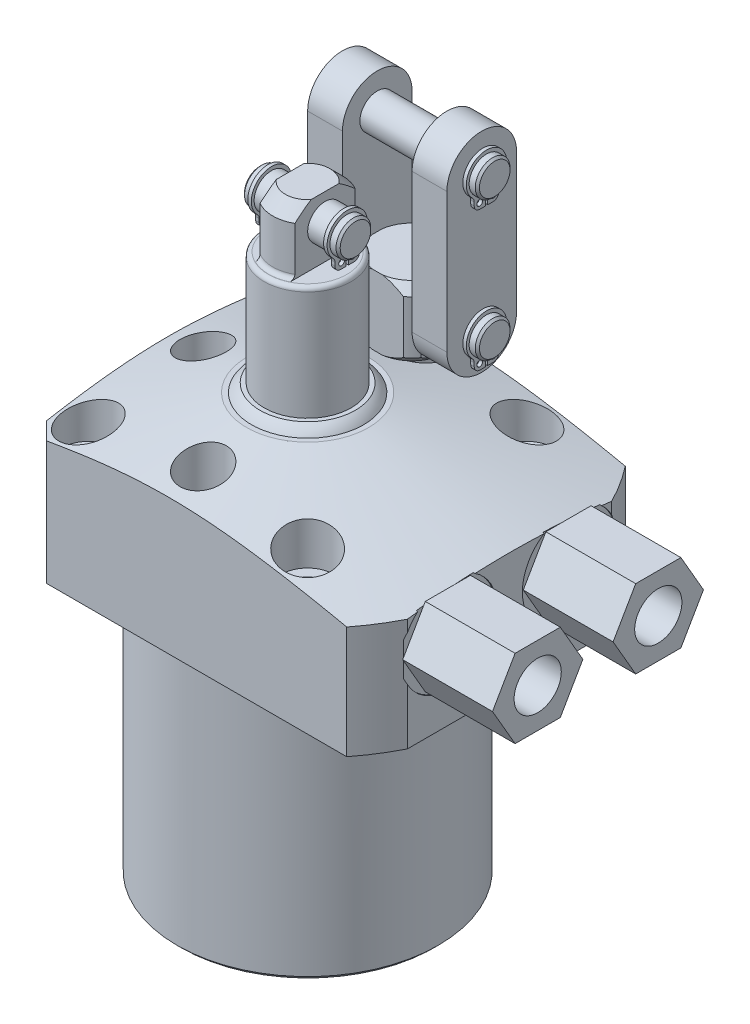
SolidWorks part; units mm, degrees
material "Alloy Steel"
ref_plane "Front Plane" through (0, 0, 0) normal (0, 0, 1) x (1, 0, 0)
ref_plane "Top Plane" through (0, 0, 0) normal (0, 1, 0) x (1, 0, 0)
ref_plane "Right Plane" through (0, 0, 0) normal (1, 0, 0) x (0, 0, -1)
sketch "Sketch28" plane through (0, 0, 0) normal (0, 0, 1) x (1, 0, 0)
  line L0 (0, 0) -> (0, 146.1857) construction
  line L1 (-11.1125, 28.575) -> (-41.275, 20.493)
  line L2 (-41.275, 20.493) -> (-41.275, 0)
  line L3 (-41.275, 0) -> (-23.8125, 0)
  line L6 (-23.8125, 0) -> (-23.8125, -47.625)
  line L9 (-23.8125, -47.625) -> (0, -47.625)
  line L10 (0, -47.625) -> (0, 28.575)
  line L11 (0, 28.575) -> (-11.1125, 28.575)
  dimension "D2" = 47.625
  dimension "D3" = 47.625
  dimension "D5" = 82.55
  dimension "D6" = 15
  dimension "D7" = 22.225
  dimension "D8" = 28.575
revolve "Revolve7" add sketch "Sketch28" angle 360 about L0
sketch "Sketch3" plane through (0, 28.575, 0) normal (0, 1, 0) x (-1, 0, 0)
  line L0 (25.4, -25.4) -> (-36.83, -25.4)
  line L3 (-36.83, 25.4) -> (25.4, 25.4)
  line L4 (25.4, -25.4) -> (25.4, 25.4)
  line L5 (-36.83, -25.4) -> (-36.83, 25.4)
  line L6 (-29.7523, 0) -> (31.3525, 0) construction
  dimension "D1" = 50.8
  dimension "D2" = 36.83
  dimension "D5" = 25.4
extrude "Cut-Extrude9" cut sketch "Sketch3" against normal up to next (76.2 mm away) flip side to cut
chamfer "Chamfer8" distance 3.175 angle 45 2 edges at (-25.4, 10.9638, -25.4) (-25.4, 10.9638, 25.4)
chamfer "Chamfer5" distance 0.762 angle 45 1 edges at (0, -47.625, -23.8125)
hole_wizard "Hole1" positions "Sketch32" profile "Sketch31" legacy
sketch "Sketch32" plane through (0, 28.575, 0) normal (0, 1, 0) x (-1, 0, 0)
  line L1 (0, 0) -> (-56.2722, 0) construction
  line L2 (0, 0) -> (0, 46.6984) construction
  point P11 (-20.0025, -20.0025)
  point P23 (-20.0025, 20.0025)
  point P25 (20.0025, -20.0025)
  point P26 (20.0025, 20.0025)
  dimension "D1" = 40.005
  dimension "D2" = 40.005
sketch "Sketch31" plane through (20.0025, 28.575, -20.0025) normal (1, 0, 0) x (0, 0, 1)
  line L0 (0, 0) -> (0, 28.575)
  line L1 (0, 28.575) -> (2.7813, 28.575)
  line L2 (2.7813, 28.575) -> (2.7813, 11.0998)
  line L3 (2.7813, 11.0998) -> (4.7625, 11.0998)
  line L4 (4.7625, 11.0998) -> (4.7625, 0)
  line L5 (4.7625, 0) -> (0, 0)
  line L6 (0, 110) -> (0, -10) construction
  dimension "Diameter" = 5.5626
  dimension "Depth" = 28.575
  dimension "C-Bore Diameter" = 9.525
  dimension "C-Bore Depth" = 11.0998
sketch "Sketch34" plane through (0, 28.575, 0) normal (0, 1, 0) x (1, 0, 0)
  line L0 (0, 0) -> (-28.6526, 0) construction
  circle A0 centre (0, 19.05) radius 4.2164
  circle A1 centre (0, -19.05) radius 4.2164
  circle A2 centre (0, 0) radius 19.05 construction
  circle A3 centre (-19.05, 0) radius 4.2164
  dimension "D1" = 8.4328
  dimension "D2" = 19.05
extrude "Cut-Extrude10" cut sketch "Sketch34" against normal blind 12.7
ref_plane "Plane23" through (0, 14.2748, 0) normal (0, -1, 0) x (1, 0, 0)
sketch "S2D0007" plane through (0, 14.2748, 0) normal (0, -1, 0) x (1, 0, 0)
  line L0 (36.83, -10.9982) -> (36.83, -19.6596)
  line L1 (36.83, -19.6596) -> (36.576, -19.6596)
  line L2 (36.576, -19.6596) -> (36.576, -15.5765)
  line L3 (36.576, -15.5765) -> (34.5059, -15.1365)
  line L4 (34.5059, -15.1365) -> (33.822, -14.4526)
  line L5 (33.822, -14.4526) -> (24.384, -14.4526)
  line L6 (24.384, -14.4526) -> (22.3084, -10.9982)
  line L7 (22.3084, -10.9982) -> (36.83, -10.9982)
  line L8 (-11.7468, -10.9982) -> (-12.1894, -10.9982) construction
  line L10 (36.83, -18.6327) -> (36.83, 18.6327) construction
  dimension "D1" = 9.1567
  dimension "D2" = 59
  dimension "D3" = 6.9088
  dimension "D4" = 45
  dimension "D5" = 12
  dimension "D6" = 2.0701
  dimension "D7" = 0.254
  dimension "D8" = 17.3228
  dimension "D9" = 10.9982
  dimension "D10" = 12.192
revolve "Cut-Revolve2" cut sketch "S2D0007" angle 360 about L8
ref_plane "Plane24" through (0, 0, -10.9982) normal (0, 0, 1) x (1, 0, 0)
sketch "Sketch6" plane through (0, 0, -10.9982) normal (0, 0, 1) x (1, 0, 0)
  line L0 (32.5341, 0) -> (-22.225, 0) construction
  line L1 (35.668, 0) -> (35.668, 1.4478)
  line L2 (35.668, 1.4478) -> (32.6075, 1.4478)
  line L3 (32.5341, 0) -> (36.83, 0) construction
  line L5 (29.9974, 0.5588) -> (31.1404, 0.5588)
  line L6 (29.9974, 0) -> (35.668, 0)
  line L8 (29.9974, 0.5588) -> (29.9974, 0)
  line L9 (29.9974, -21.0492) -> (29.9974, 0.6686) construction
  arc A1 (31.1404, 0.5588) -> (32.6075, 1.4478) centre (29.9974, 4.1) ccw
  dimension "D8" = 3.7211
  dimension "D1" = 1.4478
  dimension "D2" = 29.9974
  dimension "D7" = 0.5588
  dimension "D9" = 11.3411
  dimension "D10" = 2.286
revolve "Cut-Revolve3" cut sketch "Sketch6" angle 360 about L9
sketch "Sketch39" plane through (36.576, 0, 0) normal (1, 0, 0) x (0, 0, -1)
  line L1 (19.2398, 14.2748) -> (15.119, 21.4122)
  line L2 (15.119, 21.4122) -> (6.8774, 21.4122)
  line L3 (6.8774, 21.4122) -> (2.7566, 14.2748)
  line L4 (2.7566, 14.2748) -> (6.8774, 7.1374)
  line L5 (6.8774, 7.1374) -> (15.119, 7.1374)
  line L6 (15.119, 7.1374) -> (19.2398, 14.2748)
  circle A0 centre (10.9982, 14.2748) radius 7.1374 construction
  dimension "D1" = 14.2748
extrude "Extrude14" add sketch "Sketch39" along normal blind 16.383
hole_wizard "Hole2" positions "Sketch41" profile "Sketch40" legacy
sketch "Sketch41" plane through (52.959, 0, 0) normal (1, 0, 0) x (0, 0, -1)
  arc A0 (6.3827, 21.604) -> (19.1265, 11.283) centre (10.9982, 14.2748) ccw construction
  point P0 (10.9982, 14.2748)
sketch "Sketch40" plane through (52.959, 14.2748, -10.9982) normal (0, 1, 0) x (0, 0, -1)
  line L0 (0, 0) -> (0, 6.7056)
  line L1 (0, 6.7056) -> (4.3053, 6.7056)
  line L2 (4.3053, 6.7056) -> (4.3053, 0)
  line L3 (4.3053, 0) -> (0, 0)
  line L4 (0, 110) -> (0, -10) construction
  dimension "Diameter" = 8.6106
  dimension "Depth" = 6.7056
mirror "Mirror6" about plane through (0, 0, 0) normal (0, 0, 1) of "Hole2", "Extrude14", "Cut-Revolve2", "Cut-Revolve3"
sketch "Sketch33" plane through (0, 0, -10.9982) normal (0, 0, 1) x (1, 0, 0)
  line L0 (29.9974, 8.3297) -> (29.9974, -4.9597) construction
  line L1 (29.9974, 2.4904) -> (29.9974, -1.971) construction
  line L2 (24.3268, 1.4478) -> (35.668, 1.4478) construction
  circle A0 centre (25.2159, 0.5842) radius 0.889
  dimension "D3" = 1.778
  dimension "D1" = 9.5631
  dimension "D2" = 0.8636
revolve "Revolve9" add sketch "Sketch33" angle 360 about L0
mirror "Mirror7" about plane through (0, 0, 0) normal (0, 0, 1) of bodies 147
sketch "Sketch12" plane through (0, 0, 0) normal (0, 0, -1) x (-1, 0, 0)
  line L0 (0, 28.575) -> (0, 30.099)
  line L1 (0, 30.099) -> (8.6995, 30.099)
  line L2 (0, 28.575) -> (10.2235, 28.575)
  line L3 (0, 22.1056) -> (0, 27.6194) construction
  line L4 (11.1125, 28.575) -> (-11.1125, 28.575) construction
  arc A0 (10.2235, 28.575) -> (8.6995, 30.099) centre (6.1905, 26.066) ccw
  dimension "D1" = 4.7498
  dimension "D2" = 1.524
  dimension "D3" = 17.399
  dimension "D4" = 20.447
revolve "Revolve2" add sketch "Sketch12" angle 360 about L3
ref_plane "Plane25" through (0, 0, 0) normal (-1, 0, 0) x (0, 0, 1)
sketch "Sketch13" plane through (0, 0, 0) normal (0, 0, 1) x (1, 0, 0)
  line L0 (0, 30.099) -> (0, 61.8998)
  line L1 (0, 61.8998) -> (4.064, 61.8998)
  line L2 (4.064, 61.8998) -> (6.35, 59.6138)
  line L3 (6.35, 50.8) -> (6.35, 59.6138)
  line L4 (7.9312, 30.099) -> (0, 30.099)
  line L5 (0, 23.0264) -> (0, 64.961) construction
  line L6 (-6.0362, 57.15) -> (17.7755, 57.15) construction
  line L7 (8.6995, 30.099) -> (-8.6995, 30.099) construction
  line L8 (32.5341, 0) -> (-22.225, 0) construction
  line L10 (6.35, 50.8) -> (7.9311, 50.8)
  line L11 (7.9311, 50.8) -> (7.9312, 30.099)
  dimension "D1" = 4.7498
  dimension "D2" = 57.15
  dimension "D3" = 12.7
  dimension "D4" = 45
  dimension "D5" = 2.286
  dimension "D6" = 15.8623
  dimension "D7" = 11.0998
revolve "Revolve3" add sketch "Sketch13" angle 360 about L5
sketch "Sketch14" plane through (0, 61.8998, 0) normal (0, 1, 0) x (-1, 0, 0)
  line L0 (3.175, 5.4993) -> (3.175, -5.4993)
  line L2 (-3.175, -5.4993) -> (-3.175, 5.4993)
  line L4 (0, 0) -> (0, 0.0035) construction
  line L5 (0, -34.2265) -> (0, 34.2265) construction
  circle A0 centre (0, 0) radius 6.35 construction
  arc A1 (3.175, -5.4993) -> (3.175, 5.4993) centre (0, 0) ccw
  arc A2 (-3.175, 5.4993) -> (-3.175, -5.4993) centre (0, 0) ccw
  dimension "D1" = 6.35
extrude "Cut-Extrude7" cut sketch "Sketch14" against normal up to surface (11.0998 mm away) up to face at (0, 50.8, -6.35)
fillet "Fillet4" radius 0.762 3 edges at (0, 50.8, -7.9311) (0, 50.8, -6.35) (0, 50.8, 6.35)
sketch "Sketch29" plane through (0, 0, 0) normal (-1, 0, 0) x (0, 0, 1)
  line L0 (-2.5368, 61.8998) -> (-4.064, 61.8998) construction
  circle A0 centre (0, 57.15) radius 3.1686
  dimension "D1" = 6.3373
  dimension "D2" = 4.7498
extrude "Extrude11" add sketch "Sketch29" along normal mid plane 17.4498
sketch "Sketch16" plane through (-8.7249, 52.3748, 0) normal (-1, 0, 0) x (0, 0, 1)
  line L0 (0.2083, 1.8616) -> (0.2083, -0.1704)
  line L1 (2.2403, 1.5036) -> (2.2403, 0.871)
  line L2 (1.1989, -0.1704) -> (0.2083, -0.1704)
  line L3 (-2.2403, 1.5036) -> (-2.2403, 0.871)
  line L4 (-1.1989, -0.1704) -> (-0.2083, -0.1704)
  line L5 (-0.2083, 1.8616) -> (-0.2083, -0.1704)
  line L6 (0, -3.8062) -> (0, 3.1748) construction
  arc A0 (0.2083, 1.8616) -> (-0.2083, 1.8616) centre (0, 4.7752) ccw
  arc A1 (2.5583, 2.2527) -> (-2.5583, 2.2527) centre (0, 4.9022) ccw
  arc A2 (2.5583, 2.2527) -> (2.2403, 1.5036) centre (3.2817, 1.5036) ccw
  arc A3 (1.1989, -0.1704) -> (2.2403, 0.871) centre (1.1989, 0.871) ccw
  circle A4 centre (1.0414, 0.871) radius 0.5207
  arc A5 (-2.5583, 2.2527) -> (-2.2403, 1.5036) centre (-3.2817, 1.5036) cw
  arc A6 (-1.1989, -0.1704) -> (-2.2403, 0.871) centre (-1.1989, 0.871) cw
  circle A7 centre (-1.0414, 0.871) radius 0.5207
  circle A8 centre (0, 4.7752) radius 3.1686 construction
  dimension "D1" = 3.683
  dimension "D4" = 1.0414
  dimension "D6" = 1.0414
  dimension "D7" = 2.032
  dimension "D8" = 2.921
  dimension "D10" = 1.0414
  dimension "D11" = 1.0414
  dimension "D2" = 2.032
  dimension "D3" = 0.127
  dimension "D5" = 1.0414
  dimension "D9" = 0.4166
extrude "Extrude2" add sketch "Sketch16" against normal blind 0.635 from offset 1.4986
chamfer "Chamfer6" distance 0.381 angle 45 2 edges at (8.7249, 57.15, 3.1687) (-8.7249, 57.15, 3.1686)
mirror "Mirror2" about plane through (0, 0, 0) normal (-1, 0, 0) of "Extrude2"
sketch "Sketch35" plane through (0, 0, 0) normal (-1, 0, 0) x (0, 0, 1)
  line L0 (-19.05, 43.5741) -> (-19.05, 11.6793) construction
  line L1 (-19.05, 15.875) -> (-14.2875, 15.875)
  line L2 (-14.2875, 15.875) -> (-14.2875, 28.575)
  line L3 (-14.2875, 28.575) -> (-12.6365, 28.575)
  line L4 (-11.1125, 30.099) -> (-11.1125, 39.751)
  line L5 (-12.6365, 41.275) -> (-19.05, 41.275)
  line L6 (-19.05, 41.275) -> (-19.05, 15.875)
  line L7 (11.1125, 28.575) -> (-11.1125, 28.575) construction
  line L8 (-11.1125, 39.751) -> (-12.6365, 41.275)
  line L9 (-12.6365, 28.575) -> (-11.1125, 30.099)
  point P6 (-11.1125, 28.575)
  point P7 (-11.1125, 41.275)
  dimension "D1" = 12.7
  dimension "D2" = 9.525
  dimension "D3" = 15.875
  dimension "D4" = 25.4
  dimension "D5" = 12.7
  dimension "D6" = 19.05
  dimension "D9" = 1.524
  dimension "D10" = 1.524
revolve "Revolve10" add sketch "Sketch35" angle 360 about L0
sketch "Sketch36" plane through (0, 41.275, 0) normal (0, 1, 0) x (1, 0, 0)
  line L0 (0, 19.05) -> (-19.05, 19.05) construction
  line L1 (6.35, 23.8125) -> (6.35, 14.2875)
  line L2 (4.7625, 25.4) -> (-4.7625, 25.4)
  line L3 (-6.35, 23.8125) -> (-6.35, 14.2875)
  line L4 (4.7625, 12.7) -> (-4.7625, 12.7)
  line L5 (0, 19.05) -> (0, 0) construction
  line L6 (0, 34.2265) -> (0, -34.2265) construction
  circle A0 centre (0, 19.05) radius 7.9375 construction
  arc A2 (4.7625, 25.4) -> (-4.7625, 25.4) centre (0, 19.05) ccw
  arc A3 (-6.35, 23.8125) -> (-6.35, 14.2875) centre (0, 19.05) ccw
  arc A4 (6.35, 14.2875) -> (6.35, 23.8125) centre (0, 19.05) ccw
  arc A5 (-4.7625, 12.7) -> (4.7625, 12.7) centre (0, 19.05) ccw
  dimension "D1" = 12.7
  dimension "D2" = 12.7
extrude "Cut-Extrude11" cut sketch "Sketch36" against normal up to surface (12.7 mm away) up to face at (0, 28.575, -12.6365)
sketch "Sketch30" plane through (0, 0, 0) normal (-1, 0, 0) x (0, 0, 1)
  line L0 (-25.4, 0) -> (25.4, 0) construction
  circle A0 centre (-19.05, 34.925) radius 3.1686
  dimension "D3" = 6.3373
  dimension "D1" = 34.925
  dimension "D2" = 19.05
extrude "Extrude12" add sketch "Sketch30" along normal mid plane 30.1498
sketch "Sketch19" plane through (-15.0749, 11.0998, -22.225) normal (-1, 0, 0) x (0, 0, 1)
  line L0 (3.3833, 20.9116) -> (3.3833, 18.8796)
  line L1 (5.4153, 20.5536) -> (5.4153, 19.921)
  line L2 (4.3739, 18.8796) -> (3.3833, 18.8796)
  line L3 (0.9347, 20.5536) -> (0.9347, 19.921)
  line L4 (1.9761, 18.8796) -> (2.9667, 18.8796)
  line L5 (2.9667, 20.9116) -> (2.9667, 18.8796)
  line L6 (3.175, -5.3833) -> (3.175, 4.2478) construction
  arc A0 (3.3833, 20.9116) -> (2.9667, 20.9116) centre (3.175, 23.8252) ccw
  arc A1 (5.7333, 21.3027) -> (0.6167, 21.3027) centre (3.175, 23.9522) ccw
  arc A2 (5.7333, 21.3027) -> (5.4153, 20.5536) centre (6.4567, 20.5536) ccw
  arc A3 (4.3739, 18.8796) -> (5.4153, 19.921) centre (4.3739, 19.921) ccw
  circle A4 centre (4.4247, 19.921) radius 0.5207
  arc A5 (0.6167, 21.3027) -> (0.9347, 20.5536) centre (-0.1067, 20.5536) cw
  arc A6 (1.9761, 18.8796) -> (0.9347, 19.921) centre (1.9761, 19.921) cw
  circle A7 centre (1.9253, 19.921) radius 0.5207
  circle A8 centre (3.175, 23.8252) radius 3.1686 construction
  dimension "D1" = 3.683
  dimension "D3" = 0.127
  dimension "D4" = 1.0414
  dimension "D5" = 1.0414
  dimension "D6" = 1.0414
  dimension "D9" = 2.921
  dimension "D2" = 2.032
  dimension "D7" = 0.4166
  dimension "D8" = 2.032
  dimension "D10" = 1.0414
  dimension "D11" = 1.0414
extrude "Extrude4" add sketch "Sketch19" against normal blind 0.635 from offset 1.4986
sketch "Sketch37" plane through (-6.35, 0, 0) normal (-1, 0, 0) x (0, 0, 1)
  line L0 (-25.4, 60.325) -> (-25.4, 34.925)
  line L1 (-12.7, 60.325) -> (-12.7, 34.925)
  arc A0 (-12.7, 60.325) -> (-25.4, 60.325) centre (-19.05, 60.325) ccw
  arc A1 (-25.4, 34.925) -> (-12.7, 34.925) centre (-19.05, 34.925) ccw
  dimension "D1" = 12.7
  dimension "D2" = 25.4
  dimension "D3" = 19.3128
extrude "Extrude13" add sketch "Sketch37" along normal blind 6.35
mirror "Mirror3" about plane through (0, 0, 0) normal (-1, 0, 0) of "Extrude4"
chamfer "Chamfer7" distance 0.381 angle 45 2 edges at (15.0749, 34.925, -15.8813) (-15.0749, 34.925, -15.8814)
pattern_linear "LPattern2" count 2 spacing 25.4 along (0, 1, 0) of "Extrude4", "Mirror3", "Chamfer7", "Extrude12"
mirror "Mirror8" about plane through (0, 0, 0) normal (-1, 0, 0) of "Extrude13"
